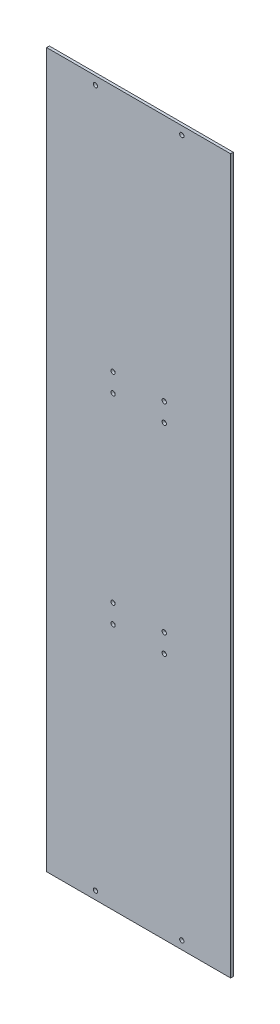
SolidWorks part; units mm, degrees
ref_plane "Front Plane" through (0, 0, 0) normal (0, 0, 1) x (1, 0, 0)
ref_plane "Top Plane" through (0, 0, 0) normal (0, 1, 0) x (1, 0, 0)
ref_plane "Right Plane" through (0, 0, 0) normal (1, 0, 0) x (0, 0, -1)
sketch "Sketch1" plane through (0, 0, 0) normal (0, 0, 1) x (1, 0, 0)
  line L1 (-53.8264, -208.915) -> (53.8264, -208.915)
  line L2 (-53.8264, -208.915) -> (-53.8264, 208.915)
  line L3 (-53.8264, 208.915) -> (53.8264, 208.915)
  line L4 (53.8264, -208.915) -> (53.8264, 208.915)
  line L5 (-53.8264, -208.915) -> (53.8264, 208.915) construction
  line L6 (-53.8264, 208.915) -> (53.8264, -208.915) construction
  point P0 (0, 0)
  dimension "D1" = 417.83
  dimension "D2" = 107.6528
extrude "Boss-Extrude1" add sketch "Sketch1" along normal blind 1.5875
sketch "Sketch2" plane through (0, 0, 0) normal (0, 0, -1) x (-1, 0, 0)
  line L0 (0, 208.915) -> (0, -208.915) construction
  line L1 (-53.8264, 208.915) -> (53.8264, 208.915) construction
  line L2 (53.8264, -208.915) -> (-53.8264, -208.915) construction
  line L3 (53.8264, -208.915) -> (-53.8264, -208.915) construction
  line L4 (53.8264, 208.915) -> (53.8264, -208.915) construction
  line L5 (53.8264, 0) -> (-53.8264, 0) construction
  line L6 (-53.8264, -208.915) -> (-53.8264, 208.915) construction
  circle A0 centre (25.2844, -204.1525) radius 1.2662
  circle A1 centre (-25.2844, -204.1525) radius 1.2662
  circle A2 centre (25.2844, 204.1525) radius 1.2662
  circle A3 centre (-25.2844, 204.1525) radius 1.2662
  dimension "D1" = 2.5324
  dimension "D2" = 4.7625
extrude "Cut-Extrude1" cut sketch "Sketch2" against normal blind 1.5875
sketch "Sketch4" plane through (0, 0, 1.5875) normal (0, 0, 1) x (1, 0, 0)
  line L0 (53.8264, 0) -> (-53.8264, 0) construction
  line L1 (53.8264, -208.915) -> (53.8264, 208.915) construction
  line L2 (-53.8264, 208.915) -> (-53.8264, -208.915) construction
  line L4 (53.8264, 208.915) -> (-53.8264, 208.915) construction
  line L5 (0, -208.915) -> (0, 208.915) construction
  line L6 (-53.8264, -208.915) -> (53.8264, -208.915) construction
  circle A0 centre (14.986, 53.086) radius 1.2662
  circle A2 centre (-14.986, 53.086) radius 1.2662
  circle A3 centre (14.986, -53.086) radius 1.2662
  circle A4 centre (-14.986, -53.086) radius 1.2662
  circle A5 centre (14.986, 64.008) radius 1.2662
  circle A6 centre (-14.986, 64.008) radius 1.2662
  circle A7 centre (14.986, -64.008) radius 1.2662
  circle A8 centre (-14.986, -64.008) radius 1.2662
  dimension "D1" = 2.5324
  dimension "D5" = 2.5324
  dimension "D2" = 14.986
  dimension "D3" = 53.086
  dimension "D4" = 10.922
  dimension "D6" = 14.986
extrude "Cut-Extrude2" cut sketch "Sketch4" against normal through all
